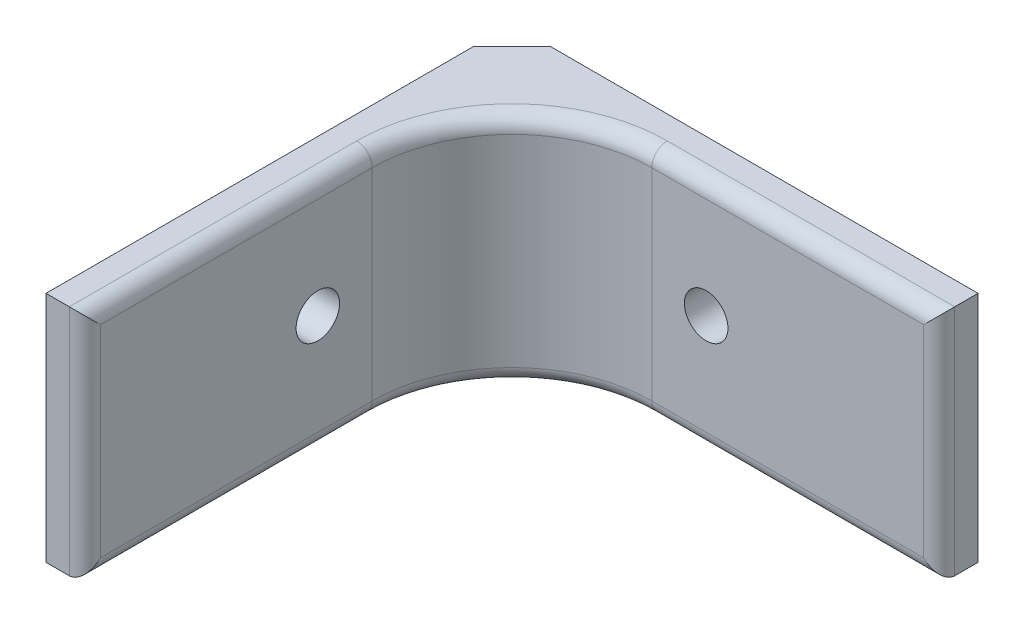
SolidWorks part; units mm, degrees
ref_plane "Front Plane" through (0, 0, 0) normal (0, 0, 1) x (1, 0, 0)
ref_plane "Top Plane" through (0, 0, 0) normal (0, 1, 0) x (1, 0, 0)
ref_plane "Right Plane" through (0, 0, 0) normal (1, 0, 0) x (0, 0, -1)
sketch "Sketch1" plane through (0, 0, 0) normal (0, 1, 0) x (1, 0, 0)
  line L0 (0, 0) -> (0, -76.2)
  line L1 (0, 0) -> (76.2, 0)
  line L2 (6.35, -6.35) -> (6.35, -76.2)
  line L3 (6.35, -6.35) -> (76.2, -6.35)
  line L4 (0, -76.2) -> (6.35, -76.2)
  line L5 (76.2, 0) -> (76.2, -6.35)
  dimension "D1" = 76.2
  dimension "D2" = 76.2
  dimension "D3" = 6.35
extrude "Boss-Extrude1" add sketch "Sketch1" along normal blind 38.1
sketch "Sketch2" plane through (6.35, 0, 0) normal (1, 0, 0) x (0, 0, -1)
  line L0 (-76.2, 19.05) -> (0, 19.05) construction
  line L1 (-76.2, 38.1) -> (-76.2, 0) construction
  line L2 (0, 38.1) -> (0, 0) construction
  circle A0 centre (-38.1, 19.05) radius 3.556
  dimension "D2" = 7.112
  dimension "D1" = 38.1
extrude "Cut-Extrude1" cut sketch "Sketch2" against normal through all
sketch "Sketch3" plane through (0, 0, 6.35) normal (0, 0, 1) x (1, 0, 0)
  line L0 (0, 19.05) -> (76.2, 19.05) construction
  line L1 (0, 38.1) -> (0, 0) construction
  line L2 (76.2, 38.1) -> (76.2, 0) construction
  circle A0 centre (38.1, 19.05) radius 3.556
  dimension "D1" = 7.112
extrude "Cut-Extrude2" cut sketch "Sketch3" against normal through all
fillet "Fillet1" radius 22.86 1 edges at (6.35, 19.05, 6.35)
fillet "Fillet2" radius 2.54 8 edges at (52.705, 0, 6.35) (6.35, 0, 52.705) (52.705, 38.1, 6.35) (13.0455, 38.1, 13.0455) (76.2, 19.05, 6.35) (6.35, 19.05, 76.2) (13.0455, 0, 13.0455) (6.35, 38.1, 52.705)
chamfer "Chamfer1" distance 6.35 angle 45 1 edges at (0, 19.05, 0)
